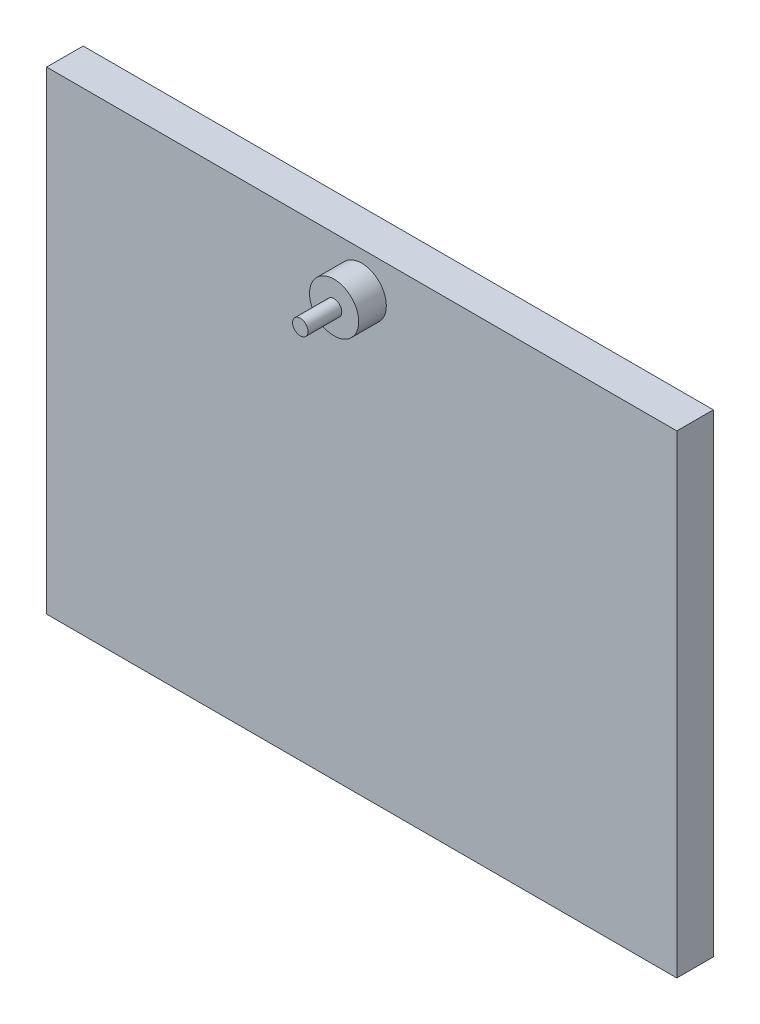
SolidWorks part; units mm, degrees
ref_plane "Front Plane" through (0, 0, 0) normal (0, 0, 1) x (1, 0, 0)
ref_plane "Top Plane" through (0, 0, 0) normal (0, 1, 0) x (1, 0, 0)
ref_plane "Right Plane" through (0, 0, 0) normal (1, 0, 0) x (0, 0, -1)
sketch "Sketch1" plane through (0, 0, 0) normal (0, 0, 1) x (1, 0, 0)
  line L1 (51.275, -38.55) -> (-51.275, -38.55)
  line L2 (51.275, -38.55) -> (51.275, 38.55)
  line L3 (51.275, 38.55) -> (-51.275, 38.55)
  line L4 (-51.275, -38.55) -> (-51.275, 38.55)
  line L5 (51.275, -38.55) -> (-51.275, 38.55) construction
  line L6 (51.275, 38.55) -> (-51.275, -38.55) construction
  point P0 (0, 0)
  dimension "D1" = 102.55
  dimension "D2" = 77.1
extrude "Boss-Extrude1" add sketch "Sketch1" along normal blind 5.94
sketch "Sketch2" plane through (0, 0, 0) normal (0, 0, -1) x (-1, 0, 0)
  line L0 (51.275, -38.55) -> (-51.275, -38.55) construction
  line L2 (-51.275, -38.55) -> (-51.275, 38.55) construction
  circle A0 centre (-30, -32.55) radius 4
  circle A1 centre (-15, -32.55) radius 4
  circle A2 centre (0, -32.55) radius 4
  circle A3 centre (15, -32.55) radius 4
  circle A4 centre (30, -32.55) radius 4
  dimension "D1" = 8
  dimension "D3" = 21.275
  dimension "D2" = 6
  dimension "D4" = 5
extrude "Boss-Extrude2" add sketch "Sketch2" along normal blind 4.5
sketch "Sketch3" plane through (0, 0, -4.5) normal (0, 0, -1) x (-1, 0, 0)
  circle A0 centre (-30, -32.55) radius 1.25
  circle A1 centre (-15, -32.55) radius 1.25
  circle A2 centre (0, -32.55) radius 1.25
  circle A3 centre (15, -32.55) radius 1.25
  circle A4 centre (30, -32.55) radius 1.25
  dimension "D1" = 2.5
  dimension "D2" = 5
extrude "Boss-Extrude3" add sketch "Sketch3" along normal blind 5.5
sketch "Sketch5" plane through (0, 0, 5.94) normal (0, 0, 1) x (1, 0, 0)
  line L0 (51.275, 38.55) -> (-51.275, 38.55) construction
  circle A0 centre (0, 32.55) radius 4
  dimension "D1" = 8
  dimension "D2" = 6
extrude "Boss-Extrude4" add sketch "Sketch5" along normal blind 4.5
sketch "Sketch6" plane through (0, 0, 10.44) normal (0, 0, 1) x (1, 0, 0)
  circle A0 centre (0, 32.55) radius 1.25
  dimension "D1" = 2.5
extrude "Boss-Extrude5" add sketch "Sketch6" along normal blind 5.5
